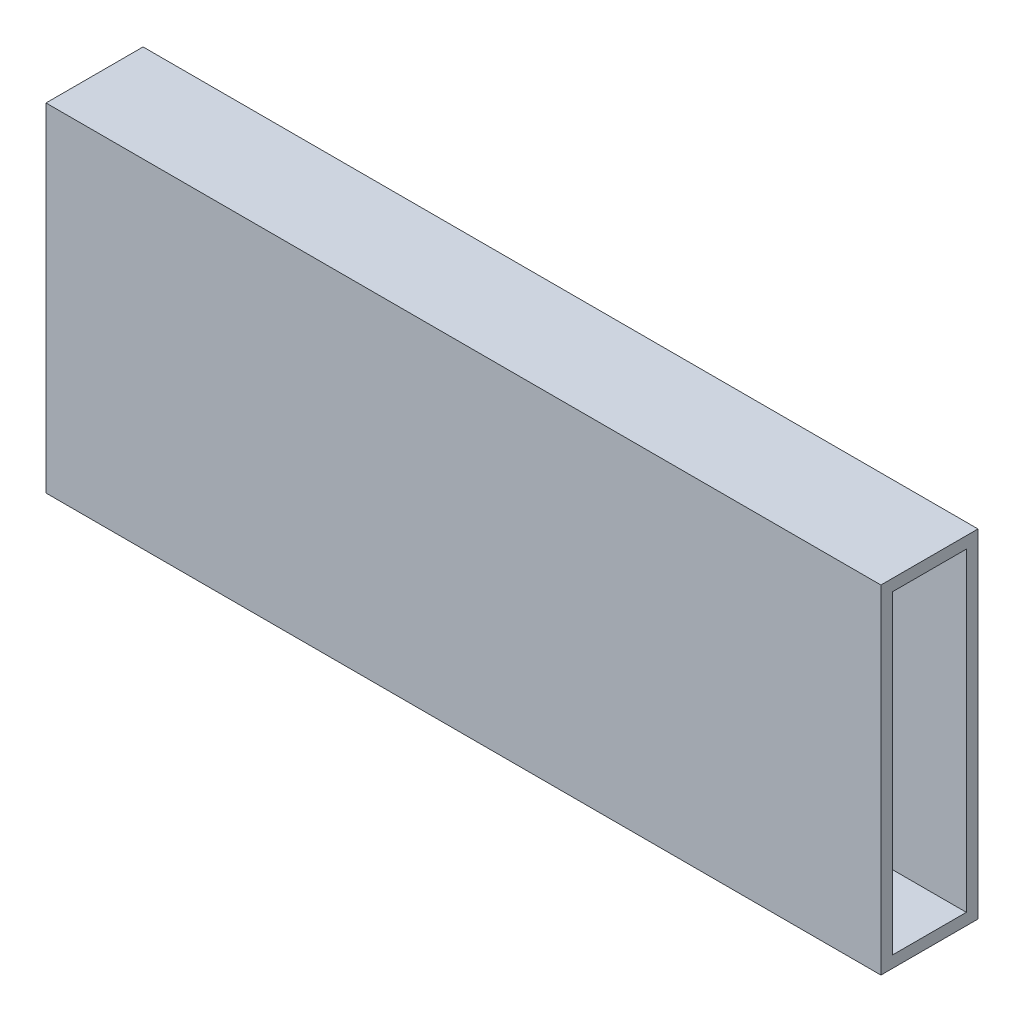
SolidWorks part; units mm, degrees
ref_plane "Front Plane" through (0, 0, 0) normal (0, 0, 1) x (1, 0, 0)
ref_plane "Top Plane" through (0, 0, 0) normal (0, 1, 0) x (1, 0, 0)
ref_plane "Right Plane" through (0, 0, 0) normal (1, 0, 0) x (0, 0, -1)
sketch "Sketch1" plane through (0, 0, 0) normal (0, 1, 0) x (1, 0, 0)
  line L1 (-107.5, 12.5) -> (107.5, 12.5)
  line L2 (-107.5, 12.5) -> (-107.5, -12.5)
  line L3 (-107.5, -12.5) -> (107.5, -12.5)
  line L4 (107.5, 12.5) -> (107.5, -12.5)
  line L5 (-107.5, 12.5) -> (107.5, -12.5) construction
  line L6 (-107.5, -12.5) -> (107.5, 12.5) construction
  point P0 (0, 0)
extrude "Boss-Extrude1" add sketch "Sketch1" along normal blind 87
sketch "Sketch3" plane through (-107.5, 0, 0) normal (-1, 0, 0) x (0, 0, 1)
  line L0 (-9.5, 84) -> (9.5, 84)
  line L1 (-9.5, 84) -> (-9.5, 3)
  line L2 (9.5, 84) -> (9.5, 3)
  line L3 (-9.5, 3) -> (9.5, 3)
  line L4 (12.5, 87) -> (12.5, 0) construction
  line L5 (-12.5, 0) -> (12.5, 0) construction
  line L6 (-12.5, 87) -> (-12.5, 0) construction
  line L7 (-12.5, 87) -> (12.5, 87) construction
  dimension "D1" = 3
  dimension "D2" = 3
  dimension "D3" = 3
  dimension "D4" = 3
extrude "Cut-Extrude1" cut sketch "Sketch3" against normal through all
sketch "Sketch4" plane through (0, 0, 0) normal (0, -1, 0) x (1, 0, 0)
  circle A0 centre (-50, 0) radius 1.5
  circle A1 centre (50, 0) radius 1.5
  dimension "D1" = 50
  dimension "D2" = 50
extrude "Cut-Extrude2" cut sketch "Sketch4" against normal blind 3
